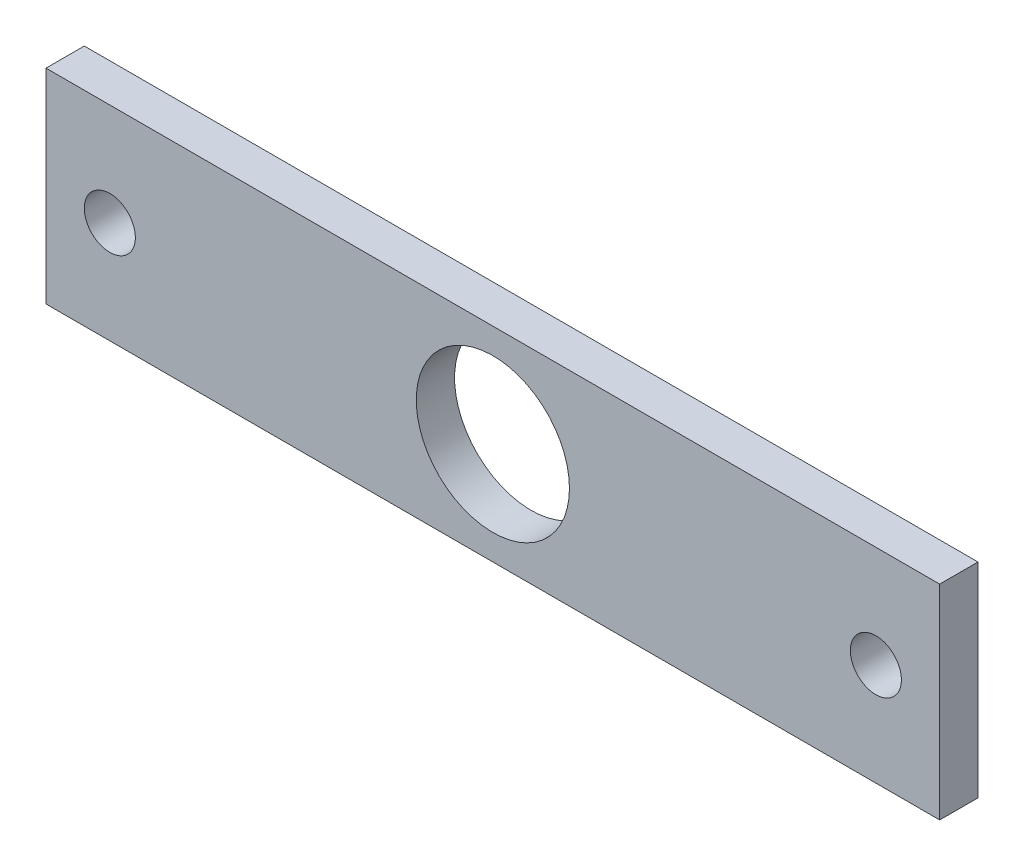
SolidWorks part; units mm, degrees
ref_plane "Alzado" through (0, 0, 0) normal (0, 0, 1) x (1, 0, 0)
ref_plane "Planta" through (0, 0, 0) normal (0, 1, 0) x (1, 0, 0)
ref_plane "Vista lateral" through (0, 0, 0) normal (1, 0, 0) x (0, 0, -1)
sketch "Croquis1" plane through (0, 0, 0) normal (0, 0, 1) x (1, 0, 0)
  line L0 (-175, 0) -> (175, 0) construction
  line L1 (-175, -40) -> (175, -40)
  line L2 (-175, -40) -> (-175, 40)
  line L3 (-175, 40) -> (175, 40)
  line L4 (175, -40) -> (175, 40)
  line L5 (-175, -40) -> (175, 40) construction
  line L6 (-175, 40) -> (175, -40) construction
  circle A0 centre (0, 0) radius 30
  circle A1 centre (150, 0) radius 10
  circle A2 centre (-150, 0) radius 10
  point P0 (0, 0)
  dimension "D3" = 60
  dimension "D4" = 20
  dimension "D5" = 20
  dimension "D1" = 350
  dimension "D2" = 80
  dimension "D6" = 300
  dimension "D7" = 25
extrude "Saliente-Extruir1" add sketch "Croquis1" against normal blind 15
